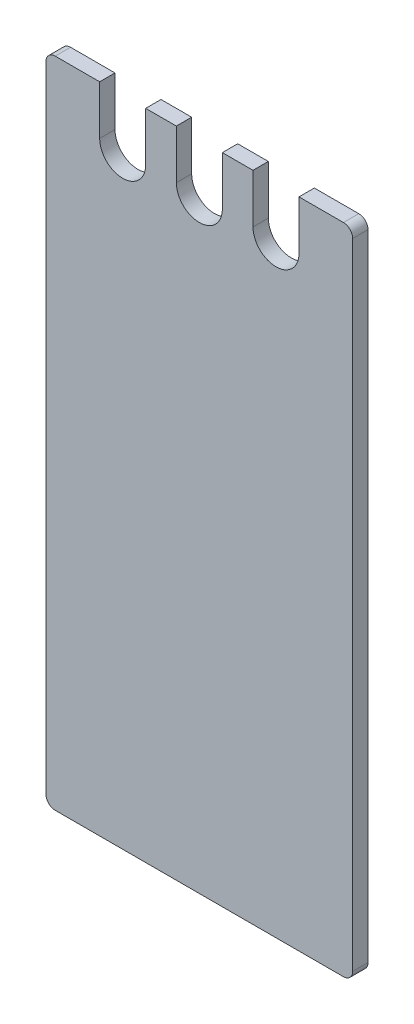
SolidWorks part; units mm, degrees
material "AISI 1045 Steel, cold drawn"
ref_plane "Front Plane" through (0, 0, 0) normal (0, 0, 1) x (1, 0, 0)
ref_plane "Top Plane" through (0, 0, 0) normal (0, 1, 0) x (1, 0, 0)
ref_plane "Right Plane" through (0, 0, 0) normal (1, 0, 0) x (0, 0, -1)
sketch "Sketch1" plane through (0, 0, 0) normal (0, 0, 1) x (1, 0, 0)
  line L0 (0, 0) -> (0, 213) construction
  line L1 (-7.5, 213) -> (-17.5, 213)
  line L2 (-7.5, 213) -> (7.5, 213) construction
  line L3 (-7.5, 213) -> (-7.5, 197)
  line L4 (-7.5, 197) -> (7.5, 197) construction
  line L5 (7.5, 213) -> (7.5, 197)
  line L6 (-50, 213) -> (-50, 0)
  line L7 (-50, 0) -> (50, 0)
  line L8 (50, 0) -> (50, 213)
  line L9 (7.5, 213) -> (17.5, 213)
  line L10 (17.5, 213) -> (17.5, 197)
  line L11 (32.5, 213) -> (32.5, 197)
  line L12 (-32.5, 213) -> (-32.5, 197)
  line L13 (-17.5, 213) -> (-17.5, 197)
  line L14 (-32.5, 213) -> (-50, 213)
  line L15 (32.5, 213) -> (50, 213)
  arc A0 (-7.5, 197) -> (7.5, 197) centre (0, 197) ccw
  arc A1 (17.5, 197) -> (32.5, 197) centre (25, 197) ccw
  arc A2 (-32.5, 197) -> (-17.5, 197) centre (-25, 197) ccw
  point P7 (0, 213)
  dimension "D2" = 15
  dimension "D1" = 213
  dimension "D3" = 16
  dimension "D4" = 100
  dimension "D5" = 2
  dimension "D6" = 2
extrude "Boss-Extrude1" add sketch "Sketch1" along normal mid plane 5
fillet "Fillet1" radius 3 4 edges at (-50, 0, 0) (50, 0, 0) (50, 213, 0) (-50, 213, 0)
